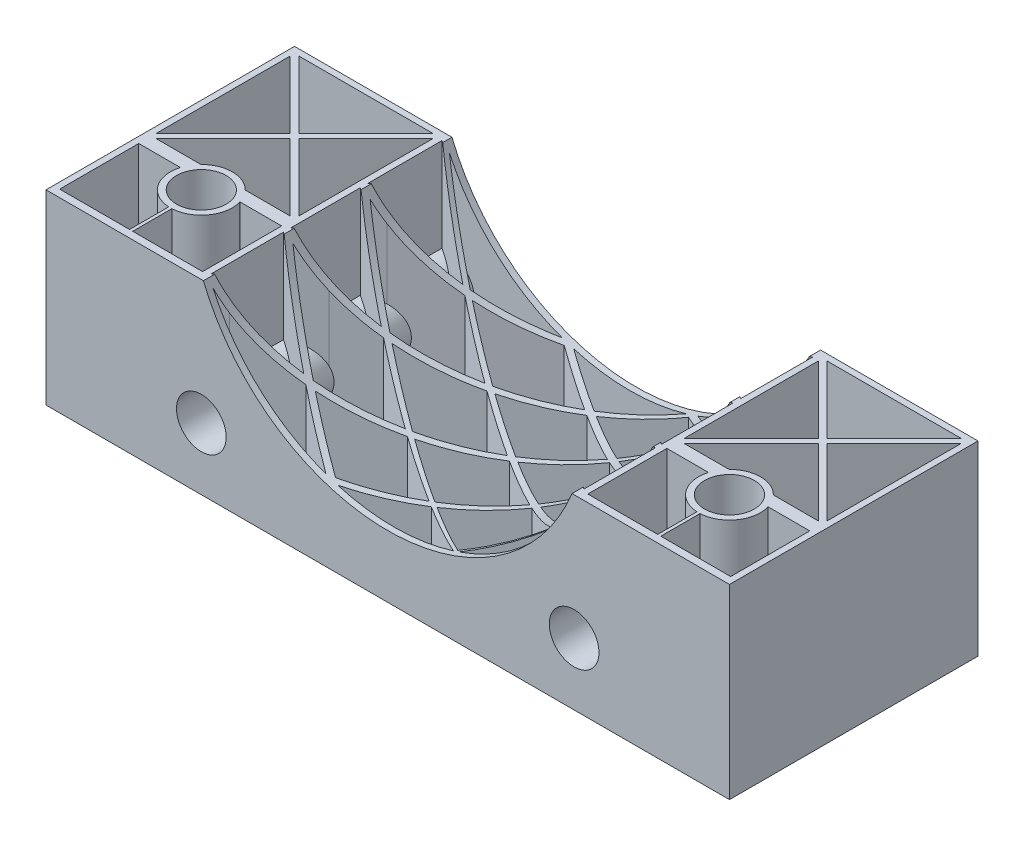
SolidWorks part; units mm, degrees
ref_plane "Front Plane" through (0, 0, 0) normal (0, 0, 1) x (1, 0, 0)
ref_plane "Top Plane" through (0, 0, 0) normal (0, 1, 0) x (1, 0, 0)
ref_plane "Right Plane" through (0, 0, 0) normal (1, 0, 0) x (0, 0, -1)
other "Center of Mass"
ref_plane "Plane1" through (55, 0, 0) normal (1, 0, 0) x (0, 0, -1)
sketch "Sketch1" plane through (0, 0, 0) normal (0, 1, 0) x (1, 0, 0)
  line L1 (0, 0) -> (110, 0)
  line L2 (0, 0) -> (0, 40)
  line L3 (0, 40) -> (110, 40)
  line L4 (110, 0) -> (110, 40)
  dimension "D1" = 110
  dimension "D2" = 40
extrude "Boss-Extrude1" add sketch "Sketch1" along normal blind 30
sketch "Sketch2" plane through (0, 0, 0) normal (0, 0, 1) x (1, 0, 0)
  line L0 (55, 0) -> (55, 10) construction
  line L1 (0, 0) -> (110, 0) construction
  line L2 (55, 10) -> (55, 42) construction
  circle A0 centre (55, 42) radius 32
  point P5 (55, 0)
  dimension "D1" = 10
  dimension "D2" = 32
extrude "Cut-Extrude1" cut sketch "Sketch2" against normal blind 40
sketch "Sketch3" plane through (0, 0, 0) normal (0, -1, 0) x (1, 0, 0)
  line L0 (110, -20) -> (85, -20) construction
  line L2 (110, 0) -> (110, -40) construction
  line L3 (0, -40) -> (0, 0) construction
  line L4 (0, -20) -> (25, -20) construction
  line L5 (0, -12.5) -> (12.5, -12.5) construction
  line L6 (12.5, -12.5) -> (12.5, 0) construction
  line L7 (0, 0) -> (110, 0) construction
  circle A0 centre (12.5, -12.5) radius 4
  dimension "D5" = 8
  dimension "D1" = 25
  dimension "D2" = 25
  dimension "D3" = 12.5
  dimension "D4" = 12.5
extrude "Cut-Extrude3" cut sketch "Sketch3" against normal blind 30
mirror "Mirror1" about plane through (55, 0, 0) normal (1, 0, 0) of "Cut-Extrude3"
sketch "Sketch7" plane through (0, 0, 0) normal (0, 0, 1) x (1, 0, 0)
  line L2 (55, -16.5) -> (55, 16.5) construction
  circle A2 centre (25, 10) radius 4
  circle A4 centre (85, 10) radius 4
  dimension "D1" = 60
extrude "Cut-Extrude6" cut sketch "Sketch7" against normal blind 40
sketch "Sketch9" plane through (0, 0, 0) normal (0, -1, 0) x (1, 0, 0)
  line L0 (12.5, -12.5) -> (12.5, 0) construction
  line L1 (0, 0) -> (110, 0) construction
  line L2 (12.5, 0) -> (12.5, -40) construction
  line L3 (110, -40) -> (0, -40) construction
  line L4 (1.7071, -39) -> (12.5, -28.2071)
  line L5 (25, 0) -> (25, -40) construction
  line L6 (1.7071, -39) -> (21.7913, -39)
  line L7 (0, -40) -> (0, 0) construction
  line L8 (25, -40) -> (0, -15) construction
  line L9 (0, -15) -> (25, -15) construction
  line L10 (25, -15) -> (0, -40) construction
  line L11 (12.5, -28.2071) -> (23.2929, -39)
  line L12 (23.2929, -39) -> (21.7913, -39)
  line L13 (1, -16.7071) -> (11.7929, -27.5)
  line L14 (1, -38.2929) -> (1, -36.7913)
  line L15 (11.7929, -27.5) -> (1, -38.2929)
  line L16 (1, -16.7071) -> (1, -36.7913)
  line L17 (23.2929, -16) -> (12.5, -26.7929)
  line L19 (12.5, -26.7929) -> (1.7071, -16)
  line L21 (24, -38.2929) -> (13.2071, -27.5)
  line L22 (24, -16.7071) -> (24, -18.2087)
  line L23 (13.2071, -27.5) -> (24, -16.7071)
  line L24 (24, -38.2929) -> (24, -18.2087)
  line L26 (1.7071, -16) -> (8.9293, -16)
  line L27 (23.2929, -16) -> (16.3426, -16) [skipped]
  line L28 (1.7071, -16) -> (3.2087, -16) [skipped]
  line L29 (16.0707, -16) -> (23.2929, -16)
  line L31 (12.25, -1.1996) -> (1, -1.1996)
  line L32 (1, -1.1996) -> (1, -13.9249)
  line L33 (12.25, -1.1996) -> (12.25, -7.5063)
  line L34 (1, -13.9249) -> (7.7073, -13.9249)
  line L35 (7.7073, -13.9249) -> (7.6892, -13.8624)
  line L36 (17.2927, -13.9249) -> (17.3108, -13.8624)
  line L37 (12.75, -1.1996) -> (12.75, -7.5063)
  line L38 (24, -13.9249) -> (17.2927, -13.9249)
  line L39 (24, -1.1996) -> (24, -13.9249)
  line L40 (12.75, -1.1996) -> (24, -1.1996)
  line L41 (55, -16.5) -> (55, 16.5) construction
  line L42 (85, -15) -> (110, -40) construction
  line L43 (110, -15) -> (85, -15) construction
  line L44 (85, -40) -> (110, -15) construction
  line L45 (85, 0) -> (85, -40) construction
  line L46 (97.5, 0) -> (97.5, -40) construction
  line L47 (97.5, -12.5) -> (97.5, 0) construction
  line L48 (97.25, -1.1996) -> (86, -1.1996)
  line L49 (86, -1.1996) -> (86, -13.9249)
  line L50 (86, -13.9249) -> (92.7073, -13.9249)
  line L51 (97.25, -1.1996) -> (97.25, -7.5063)
  line L52 (92.7073, -13.9249) -> (92.6892, -13.8624)
  line L53 (102.2927, -13.9249) -> (102.3108, -13.8624)
  line L54 (109, -13.9249) -> (102.2927, -13.9249)
  line L55 (97.75, -1.1996) -> (97.75, -7.5063)
  line L56 (109, -1.1996) -> (109, -13.9249)
  line L57 (97.75, -1.1996) -> (109, -1.1996)
  line L58 (93.9293, -16) -> (86.7071, -16)
  line L59 (108.2929, -16) -> (101.0707, -16)
  line L60 (86, -38.2929) -> (86, -18.2087)
  line L61 (96.7929, -27.5) -> (86, -16.7071)
  line L62 (86, -16.7071) -> (86, -18.2087)
  line L63 (86, -38.2929) -> (96.7929, -27.5)
  line L64 (97.5, -26.7929) -> (108.2929, -16)
  line L65 (86.7071, -16) -> (97.5, -26.7929)
  line L66 (109, -16.7071) -> (109, -36.7913)
  line L67 (98.2071, -27.5) -> (109, -38.2929)
  line L68 (109, -38.2929) -> (109, -36.7913)
  line L69 (109, -16.7071) -> (98.2071, -27.5)
  line L70 (86.7071, -39) -> (88.2087, -39)
  line L71 (97.5, -28.2071) -> (86.7071, -39)
  line L72 (108.2929, -39) -> (88.2087, -39)
  line L73 (108.2929, -39) -> (97.5, -28.2071)
  circle A1 centre (12.5, -12.5) radius 4 construction
  arc A3 (8.9293, -16) -> (16.0707, -16) centre (12.5, -12.5) ccw
  arc A5 (12.25, -7.5063) -> (7.6892, -13.8624) centre (12.5, -12.5) ccw
  arc A6 (12.75, -7.5063) -> (17.3108, -13.8624) centre (12.5, -12.5) cw
  arc A7 (97.25, -7.5063) -> (92.6892, -13.8624) centre (97.5, -12.5) ccw
  arc A8 (97.75, -7.5063) -> (102.3108, -13.8624) centre (97.5, -12.5) cw
  arc A9 (101.0707, -16) -> (93.9293, -16) centre (97.5, -12.5) cw
  point P18 (12.5, -27.5)
  point P36 (12.5, -27.5)
  point P39 (12.5, -16.5)
  point P40 (10.5635, -16)
  point P41 (14.4365, -16)
  point P50 (8.9293, -16)
  point P52 (12.25, -7.5063)
  point P53 (7.7073, -13.9249)
  point P98 (102.2927, -13.9249)
  point P99 (97.75, -7.5063)
  point P100 (101.0707, -16)
  point P101 (95.5635, -16)
  point P102 (99.4365, -16)
  point P103 (97.5, -16.5)
  point P104 (97.5, -27.5)
  dimension "D5" = 0.5
  dimension "D1" = 12.5
  dimension "D2" = 1
  dimension "D3" = 0.5
  dimension "D4" = 4
extrude "Cut-Extrude7" cut sketch "Sketch9" against normal blind 30
sketch "Sketch11" plane through (0, 0, 0) normal (0, -1, 0) x (1, 0, 0)
  line L0 (25, -1) -> (25, -39) construction
  line L1 (25, -39) -> (85, -39) construction
  line L2 (85, -39) -> (85, -1) construction
  line L3 (85, -1) -> (25, -1) construction
  line L4 (0, 0) -> (110, 0) construction
  line L5 (24, -13.9249) -> (24, -1.1996) construction
  line L6 (110, -40) -> (0, -40) construction
  line L7 (86, -16.7071) -> (86, -38.2929) construction
  line L8 (55, -1) -> (55, -39) construction
  line L9 (25, -20) -> (54, -20) construction
  line L10 (85, -1) -> (65, -1)
  line L11 (65, -1) -> (45, -1)
  line L12 (45, -1) -> (25, -1)
  line L13 (25, -1) -> (25, -13.6)
  line L14 (25, -13.6) -> (25, -26.2)
  line L15 (25, -26.2) -> (25, -39)
  line L16 (85, -39) -> (65, -39)
  line L17 (45, -39) -> (25, -39)
  line L18 (85, -39) -> (25, -39) construction
  line L19 (65, -39) -> (45, -39)
  line L20 (25, -13.8) -> (25, -1)
  line L21 (85, -26.2) -> (85, -39)
  line L22 (85, -1) -> (85, -13.6)
  line L23 (85, -13.6) -> (85, -26.2)
  line L24 (25, -13.8) -> (45, -1) construction
  line L25 (25, -26.2) -> (65, -1) construction
  line L26 (25, -39) -> (85, -1) construction
  line L27 (45, -39) -> (85, -13.6) construction
  line L28 (65, -39) -> (85, -26.2) construction
  line L29 (85, -13.6) -> (65, -1) construction
  line L30 (85, -26.2) -> (45, -1) construction
  line L31 (85, -39) -> (25, -1) construction
  line L32 (65, -39) -> (25, -13.8) construction
  line L33 (25.86, -2.1365) -> (81.8164, -37.5756)
  line L34 (25.9456, -2.1907) -> (25, -1.5918)
  line L35 (81.8164, -37.5756) -> (84.0655, -39)
  line L36 (27.2382, -1.8257) -> (83.9174, -37.7225)
  line L37 (27.5296, -2.0103) -> (25.86, -1)
  line L38 (83.9174, -37.7225) -> (85, -38.4082)
  line L39 (28.4232, -12.2028) -> (38.2658, -5.9035)
  line L40 (38.2658, -5.9035) -> (45.9276, -1)
  line L41 (37.2659, -5.3562) -> (44.0724, -1)
  line L42 (37.2659, -5.3562) -> (27.9267, -11.3333)
  line L43 (27.9267, -11.3333) -> (25, -13.2064)
  line L44 (47.7229, -3.3064) -> (79.6333, -23.4099)
  line L45 (79.6333, -23.4099) -> (85, -26.791)
  line L46 (47.7229, -3.3064) -> (44.0724, -1)
  line L47 (45.9276, -1) -> (81.2018, -23.2162)
  line L48 (81.2018, -23.2162) -> (85, -25.6083)
  line L49 (63.0254, -2.5395) -> (28.312, -24.7044)
  line L50 (28.312, -24.7044) -> (25, -26.8191)
  line L51 (28.3301, -23.5111) -> (61.7814, -2.7322)
  line L52 (61.7814, -2.7322) -> (64.5701, -1)
  line L53 (63.0254, -2.5395) -> (65.4364, -1)
  line L54 (65.4364, -1) -> (69.4058, -3.4802)
  line L55 (69.4058, -3.4802) -> (85, -13.2239)
  line L56 (64.5701, -1) -> (67.6965, -2.9943)
  line L57 (67.6965, -2.9943) -> (85, -14.0318)
  line L58 (85, -14.0318) -> (81.3497, -16.5102)
  line L59 (67.4512, -38.0249) -> (82.2284, -28.5675)
  line L60 (82.2284, -28.5675) -> (85, -26.791)
  line L61 (67.4512, -38.0249) -> (65.9299, -39)
  line L62 (65.9299, -39) -> (29.5093, -16.0499)
  line L63 (29.5093, -16.0499) -> (25, -13.2064)
  line L64 (28.0981, -16.3428) -> (62.6323, -38.0993)
  line L65 (62.6323, -38.0993) -> (64.062, -39)
  line L66 (28.0981, -16.3428) -> (25, -14.391)
  line L67 (28.3301, -23.5111) -> (25, -25.5796)
  line L68 (29.5859, -36.6874) -> (82.8637, -2.9448)
  line L69 (82.8637, -2.9448) -> (85, -1.5918)
  line L70 (78.5744, -4.4777) -> (29.2621, -36.0047)
  line L71 (29.2621, -36.0047) -> (25, -38.7297)
  line L72 (29.5859, -36.6874) -> (25.9345, -39)
  line L73 (47.1403, -38.2332) -> (81.3497, -16.5102)
  line L74 (80.4967, -15.8673) -> (46.2437, -37.6179)
  line L75 (46.2437, -37.6179) -> (44.0673, -39)
  line L76 (80.4967, -15.8673) -> (85, -13.0077)
  line L77 (78.5744, -4.4777) -> (84.014, -1)
  line L78 (47.1403, -38.2332) -> (45.9276, -39)
  line L79 (66.8535, -37.2201) -> (80.6496, -28.3906)
  line L80 (80.6496, -28.3906) -> (85, -25.6083)
  line L81 (66.8535, -37.2201) -> (64.062, -39)
  line L82 (28.4232, -12.2028) -> (25, -14.391)
  line L83 (25, -26.2) -> (45, -39) construction
  line L84 (26.8548, -27.9807) -> (42.5394, -38.0189)
  line L85 (42.5394, -38.0189) -> (44.0673, -39)
  line L86 (26.8548, -27.9807) -> (25, -26.8191)
  line L87 (27.6269, -27.2876) -> (43.5979, -37.5091)
  line L88 (43.5979, -37.5091) -> (45.9276, -39)
  line L89 (27.6269, -27.2876) -> (25, -25.5796)
  point P18 (35, 7.2209)
  point P35 (82.8637, -2.9448)
  point P37 (29.5859, -36.6874)
  point P38 (29.2621, -36.0047)
  point P39 (28.312, -24.7044)
  point P40 (28.3301, -23.5111)
  point P41 (28.0981, -16.3428)
  point P42 (29.5093, -16.0499)
  point P43 (28.4232, -12.2028)
  point P44 (27.9267, -11.3333)
  point P45 (37.2659, -5.3562)
  point P46 (38.2658, -5.9035)
  point P47 (49.0942, -2.9884)
  point P48 (47.7229, -3.3064)
  point P49 (81.2018, -23.2162)
  point P50 (79.6333, -23.4099)
  point P51 (80.6496, -28.3906)
  point P52 (82.2284, -28.5675)
  point P53 (80.4967, -15.8673)
  point P54 (81.3497, -16.5102)
  point P55 (81.5522, -11.1324)
  point P56 (81.3412, -11.8859)
  point P57 (69.4058, -3.4802)
  point P58 (67.6965, -2.9943)
  point P59 (61.7814, -2.7322)
  point P60 (63.0254, -2.5395)
  point P84 (47.1403, -38.2332)
  point P86 (46.2437, -37.6179)
  point P87 (62.6323, -38.0993)
  point P88 (67.4512, -38.0249)
  point P100 (78.5744, -4.4777)
  point P110 (66.8535, -37.2201)
  point P116 (27.6269, -27.2876)
  point P117 (26.8548, -27.9807)
  point P118 (42.5394, -38.0189)
  point P119 (43.5979, -37.5091)
  dimension "D1" = 1
  dimension "D2" = 1
  dimension "D3" = 1
  dimension "D4" = 1
  dimension "D5" = 1
  dimension "D6" = 0.5
  dimension "D7" = 0.5
  dimension "D8" = 0.5
  dimension "D9" = 0.5
  dimension "D10" = 0.5
  dimension "D11" = 0.5
  dimension "D12" = 0.5
  dimension "D13" = 0.5
  dimension "D14" = 0.5
  dimension "D15" = 0.5
  dimension "D16" = 0.5
  dimension "D17" = 0.5
  dimension "D18" = 0.5
  dimension "D19" = 0.5
  dimension "D20" = 0.5
  dimension "D21" = 0.5
  dimension "D22" = 0.5
  dimension "D23" = 0.5
  dimension "D24" = 0.5
  dimension "D25" = 0.5
  dimension "D26" = 0.5
  dimension "D27" = 0.5
  dimension "D28" = 0.5
  dimension "D29" = 0.5
  dimension "D30" = 0.5
  dimension "D31" = 0.5
  dimension "D32" = 0.5
  dimension "D33" = 0.5
  dimension "D34" = 0.5
  dimension "D35" = 0.5
  dimension "D36" = 0.5
  dimension "D37" = 0.5
  dimension "D38" = 0.5
  dimension "D39" = 0.5
  dimension "D40" = 0.5
  dimension "D41" = 0.5
  dimension "D42" = 0.5
extrude "Cut-Extrude9" cut sketch "Sketch11" against normal blind 30
sketch "Sketch12" plane through (0, 0, 0) normal (0, 0, 1) x (1, 0, 0)
  line L0 (55, -16.5) -> (55, 16.5) construction
  circle A0 centre (25, 10) radius 5
  circle A1 centre (85, 10) radius 5
  point P0 (25, 10)
  dimension "D1" = 10
extrude "Boss-Extrude3" add sketch "Sketch12" against normal blind 40
sketch "Sketch15" plane through (0, 0, 0) normal (0, 0, 1) x (1, 0, 0)
  line L0 (55, -16.5) -> (55, 16.5) construction
  circle A0 centre (25, 10) radius 4
  circle A1 centre (85, 10) radius 4
  point P0 (25, 10)
  dimension "D1" = 8
extrude "Cut-Extrude10" cut sketch "Sketch15" against normal blind 40
